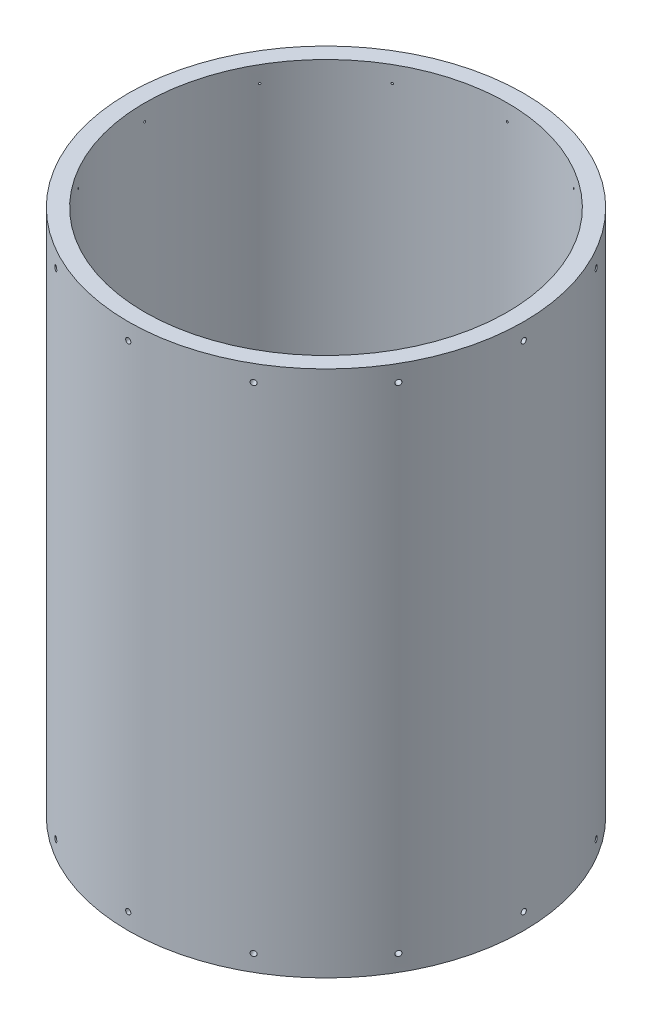
SolidWorks part; units mm, degrees
ref_plane "Front Plane" through (0, 0, 0) normal (0, 0, 1) x (1, 0, 0)
ref_plane "Top Plane" through (0, 0, 0) normal (0, 1, 0) x (1, 0, 0)
ref_plane "Right Plane" through (0, 0, 0) normal (1, 0, 0) x (0, 0, -1)
sketch "Sketch1" plane through (0, 0, 0) normal (0, 1, 0) x (1, 0, 0)
  circle A0 centre (0, 0) radius 139.7
  circle A1 centre (0, 0) radius 152.4
  dimension "D1" = 279.4
  dimension "D2" = 304.8
extrude "Boss-Extrude1" add sketch "Sketch1" along normal blind 406.4
ref_plane "Plane1" through (152.4, 0, 0) normal (1, 0, 0) x (0, 0, -1)
hole_wizard "#10-32 Tapped Hole1" positions "Sketch2" profile "Sketch3" tap size "#10-32" standard "ANSI Inch"
sketch "Sketch2" plane through (152.4, 0, 0) normal (1, 0, 0) x (0, 0, -1)
  line L0 (0, 393.7) -> (0, 0)
  line L2 (152.4, 406.4) -> (-152.4, 406.4) construction
  point P0 (0, 393.7)
  dimension "D1" = 12.7
sketch "Sketch3" plane through (152.4, 393.7, 0) normal (0, 1, 0) x (0, 0, -1)
  line L0 (0, 0) -> (0, 13.1513)
  line L1 (0, 13.1513) -> (2.0193, 11.938)
  line L2 (2.0193, 11.938) -> (2.0193, 0)
  line L5 (2.0193, 0) -> (0, 0)
  line L10 (0, 13.1513) -> (-2.0193, 11.938) construction
  line L11 (0, -6.35) -> (0, 107.95) construction
  dimension "Tap Drill Dia." = 4.0386
  dimension "Tap Drill Depth" = 11.938
  dimension "Drill Angle" = 118
cosmetic thread "Hole Thread1" parameters "D1"=9.652, "D2"=4.826
pattern_circular "CirPattern1" count 12 over 360 about axis through (0, 406.4, 0) along (0, 1, 0) of "#10-32 Tapped Hole1"
ref_plane "Plane2" through (0, 203.2, 0) normal (0, 1, 0) x (1, 0, 0)
mirror "Mirror1" about plane through (0, 203.2, 0) normal (0, 1, 0) of "CirPattern1", "#10-32 Tapped Hole1"
